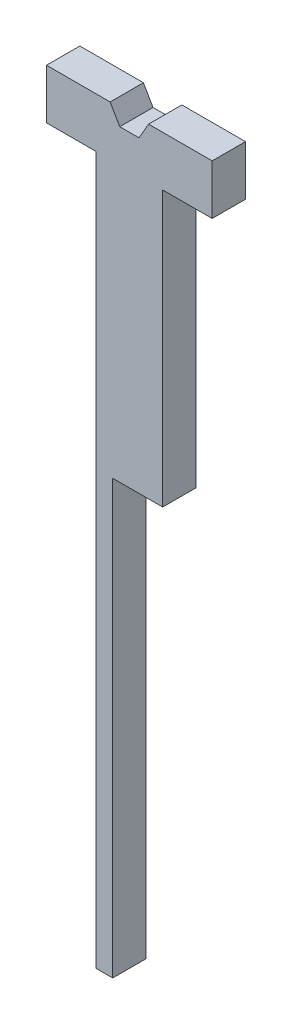
SolidWorks part; units mm, degrees
ref_plane "Front Plane" through (0, 0, 0) normal (0, 0, 1) x (1, 0, 0)
ref_plane "Top Plane" through (0, 0, 0) normal (0, 1, 0) x (1, 0, 0)
ref_plane "Right Plane" through (0, 0, 0) normal (1, 0, 0) x (0, 0, -1)
sketch "Sketch1" plane through (0, 0, 0) normal (0, 0, 1) x (1, 0, 0)
  line L0 (-10, -22.5) -> (10, -22.5)
  line L1 (-24.875, -7.5) -> (24.875, -7.5)
  line L2 (-24.875, -7.5) -> (-24.875, 7.5)
  line L3 (-24.875, 7.5) -> (24.875, 7.5)
  line L4 (24.875, -7.5) -> (24.875, 7.5)
  line L5 (-24.875, -7.5) -> (24.875, 7.5) construction
  line L6 (-24.875, 7.5) -> (24.875, -7.5) construction
  line L7 (-10, -22.5) -> (10, -22.5)
  line L8 (-10, -22.5) -> (-10, 7.5)
  line L9 (-10, 7.5) -> (10, 7.5)
  line L10 (10, -22.5) -> (10, 7.5)
  line L11 (-10, -22.5) -> (10, 7.5) construction
  line L12 (-10, 7.5) -> (10, -22.5) construction
  line L13 (5.7735, 7.5) -> (2.8868, 12.5)
  line L14 (2.8868, 12.5) -> (-2.8868, 12.5)
  line L15 (-2.8868, 12.5) -> (-5.7735, 7.5)
  line L16 (-5.7735, 7.5) -> (-2.8868, 2.5)
  line L17 (-2.8868, 2.5) -> (2.8868, 2.5)
  line L18 (2.8868, 2.5) -> (5.7735, 7.5)
  line L19 (-10, -22.5) -> (-10, -220)
  line L20 (10, -22.5) -> (10, -220)
  line L21 (-10, -220) -> (10, -220)
  circle A0 centre (0, 7.5) radius 5 construction
  point P0 (0, 0)
  point P6 (0, -7.5)
  dimension "D1" = 49.75
  dimension "D2" = 20
  dimension "D3" = 10
extrude "Boss-Extrude1" add sketch "Sketch1" along normal blind 10 contours L19 L21 L20 L0 | L0 L10 L1 L8 | L18 L17 L16 L3 L8 L1 L10 L9 | L1 L8 L3 L2 | L10 L1 L4 L3
sketch "Çizim1" plane through (10, 0, 0) normal (1, 0, 0) x (0, 0, -1)
  line L0 (0, -220) -> (-10, -220)
  line L1 (0, -220) -> (0, -90)
  line L2 (-10, -220) -> (-10, -90)
  line L3 (0, -90) -> (-10, -90)
extrude "Kes-Ekstrüzyon1" cut sketch "Çizim1" against normal blind 15
